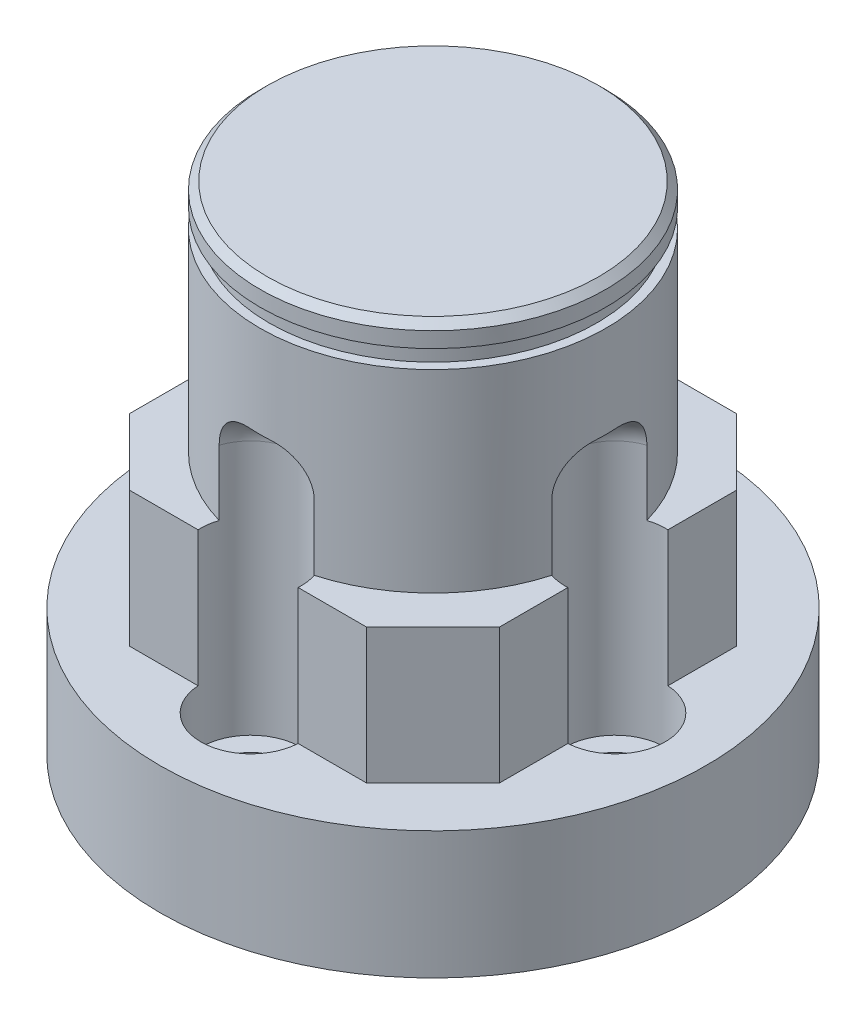
SolidWorks part; units mm, degrees
ref_plane "Front Plane" through (0, 0, 0) normal (0, 0, 1) x (1, 0, 0)
ref_plane "Top Plane" through (0, 0, 0) normal (0, 1, 0) x (1, 0, 0)
ref_plane "Right Plane" through (0, 0, 0) normal (1, 0, 0) x (0, 0, -1)
sketch "Sketch1" plane through (0, 0, 0) normal (0, 1, 0) x (1, 0, 0)
  circle A0 centre (0, 0) radius 15
  circle A1 centre (0, 0) radius 10 construction
  circle A2 centre (0, 10) radius 1.6
  circle A3 centre (0, -10) radius 1.6
  circle A4 centre (10, 0) radius 1.6
  circle A5 centre (-10, 0) radius 1.6
  dimension "D1" = 30
  dimension "D2" = 20
  dimension "D3" = 3.2
extrude "Boss-Extrude1" add sketch "Sketch1" along normal blind 7
sketch "Sketch2" plane through (0, 7, 0) normal (0, 1, 0) x (1, 0, 0)
  line L5 (-6.505, 10.155) -> (6.505, 10.155)
  line L6 (-10.155, -10.155) -> (10.155, -10.155) construction
  line L10 (-10.155, -10.155) -> (-10.155, 10.155) construction
  line L11 (-10.155, 10.155) -> (10.155, 10.155) construction
  line L12 (10.155, -10.155) -> (10.155, 10.155) construction
  line L13 (-10.155, -10.155) -> (10.155, 10.155) construction
  line L14 (-10.155, 10.155) -> (10.155, -10.155) construction
  line L15 (6.505, 10.155) -> (10.155, 6.505)
  line L16 (10.155, 6.505) -> (10.155, -6.505)
  line L17 (10.155, -6.505) -> (6.505, -10.155)
  line L18 (6.505, -10.155) -> (-6.505, -10.155)
  line L19 (-6.505, -10.155) -> (-10.155, -6.505)
  line L20 (-10.155, -6.505) -> (-10.155, 6.505)
  line L21 (-10.155, 6.505) -> (-6.505, 10.155)
  point P0 (0, 0)
  dimension "D1" = 20.31
  dimension "D2" = 13.01
extrude "Boss-Extrude2" add sketch "Sketch2" along normal blind 7.42
sketch "Sketch3" plane through (0, 14.42, 0) normal (0, 1, 0) x (1, 0, 0)
  circle A0 centre (0, 0) radius 9.5
  dimension "D1" = 19
extrude "Boss-Extrude3" add sketch "Sketch3" along normal blind 12.88
sketch "Sketch4" plane through (0, 0, 0) normal (0, 0, 1) x (1, 0, 0)
  line L0 (9.5, 14.42) -> (9.5, 27.3) construction
  line L1 (9, 25.05) -> (10, 25.05)
  line L2 (9, 25.05) -> (9, 25.7613)
  line L3 (9.5, 26.05) -> (10, 26.05)
  line L4 (10, 25.05) -> (10, 26.05)
  line L5 (9, 25.05) -> (10, 26.05) construction
  line L6 (9, 26.05) -> (10, 25.05) construction
  line L7 (9.5, 27.3) -> (-9.5, 27.3) construction
  line L8 (0, 27.3) -> (0, 0) construction
  line L9 (9, 25.7613) -> (9.5, 26.05)
  line L10 (9.5, 27.3) -> (9.5, 26.05) construction
  point P0 (9.5, 25.55)
  dimension "D1" = 1.25
  dimension "D2" = 1
  dimension "D3" = 1
  dimension "D4" = 60
  dimension "D5" = 0.7113
  dimension "D6" = 0.5
revolve "Cut-Revolve1" cut sketch "Sketch4" angle 360 about L8
sketch "Sketch5" plane through (0, 0, 0) normal (0, -1, 0) x (1, 0, 0)
  circle A0 centre (0, -10) radius 1.6 construction
  circle A1 centre (10, 0) radius 1.6 construction
  circle A2 centre (-10, 0) radius 1.6 construction
  circle A3 centre (0, 10) radius 1.6 construction
  circle A4 centre (0, -10) radius 1.6
  circle A5 centre (10, 0) radius 1.6
  circle A6 centre (-10, 0) radius 1.6
  circle A7 centre (0, 10) radius 1.6
extrude "Cut-Extrude1" cut sketch "Sketch5" against normal blind 20
sketch "Sketch6" plane through (0, 20, 0) normal (0, -1, 0) x (1, 0, 0)
  circle A0 centre (10, 0) radius 2.75
  circle A1 centre (0, 10) radius 2.75
  circle A2 centre (-10, 0) radius 2.75
  circle A3 centre (0, -10) radius 2.75
  dimension "D1" = 5.5
extrude "Cut-Extrude2" cut sketch "Sketch6" along normal offset from surface (16 mm away) 3 up to face at (0, 7, 0) offset beyond the face yes
fillet "Fillet1" radius 2 4 edges at (0, 20, 7.25) (-7.25, 20, 0) (0, 20, -7.25) (7.25, 20, 0)
chamfer "Chamfer1" distance 0.4 angle 45 1 edges at (0, 27.3, 9.5)
